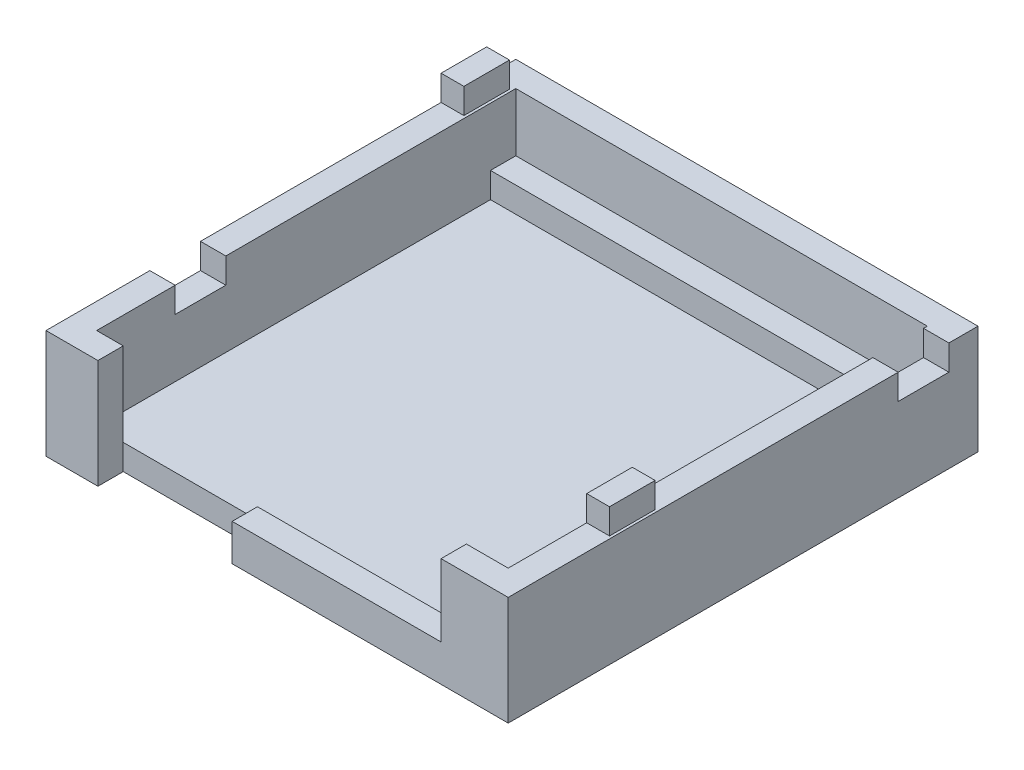
SolidWorks part; units mm, degrees
ref_plane "Front Plane" through (0, 0, 0) normal (0, 0, 1) x (1, 0, 0)
ref_plane "Top Plane" through (0, 0, 0) normal (0, 1, 0) x (1, 0, 0)
ref_plane "Right Plane" through (0, 0, 0) normal (1, 0, 0) x (0, 0, -1)
sketch "Sketch3" plane through (0, 0, 0) normal (0, 1, 0) x (1, 0, 0)
  line L1 (0, 0) -> (36.5, 0)
  line L2 (0, 0) -> (0, -37.1)
  line L3 (0, -37.1) -> (36.5, -37.1)
  line L4 (36.5, 0) -> (36.5, -37.1)
  dimension "D1" = 37.1
  dimension "D2" = 36.5
extrude "Shell" add sketch "Sketch3" along normal blind 8.6
sketch "Sketch4" plane through (0, 8.6, 0) normal (0, 1, 0) x (1, 0, 0)
  line L0 (36.5, 0) -> (0, 0) construction
  line L1 (2, -4) -> (34.5, -4)
  line L2 (2, -4) -> (2, -35.1)
  line L3 (2, -35.1) -> (34.5, -35.1)
  line L4 (34.5, -4) -> (34.5, -35.1)
  line L5 (36.5, -37.1) -> (36.5, 0) construction
  line L6 (0, 0) -> (0, -37.1) construction
  line L7 (0, -37.1) -> (36.5, -37.1) construction
  dimension "D1" = 4
  dimension "D2" = 2
  dimension "D3" = 2
  dimension "D4" = 2
extrude "Main Cavity" cut sketch "Sketch4" against normal offset from surface (6.6 mm away) 2 up to face at (18.25, 0, 18.55)
sketch "Sketch5" plane through (0, 8.6, 0) normal (0, 1, 0) x (1, 0, 0)
  line L0 (34.5, -35.1) -> (34.5, -4) construction
  line L1 (2, -4) -> (34.5, -4)
  line L2 (2, -4) -> (2, -2)
  line L3 (2, -2) -> (34.5, -2)
  line L4 (34.5, -4) -> (34.5, -2)
  dimension "D1" = 2
extrude "Support Shelf" cut sketch "Sketch5" against normal offset from surface (4.6 mm away) 2 up to face at (18.25, 2, 19.55)
sketch "Sketch6" plane through (0, 0, 37.1) normal (0, 0, 1) x (1, 0, 0)
  line L0 (0, 0) -> (36.5, 0) construction
  line L2 (31.2, 2.9) -> (31.2, 8.6)
  line L10 (14.7, 0) -> (4.1, 0)
  line L13 (4.1, 0) -> (4.1, 8.6)
  line L14 (0, 8.6) -> (0, 0) construction
  line L18 (14.7, 0) -> (14.7, 2.9)
  line L19 (14.7, 2.9) -> (31.2, 2.9)
  line L20 (31.2, 8.6) -> (4.1, 8.6)
  dimension "D1" = 4.1
  dimension "D2" = 2.9
  dimension "D6" = 10.6
extrude "Terminal Input" cut sketch "Sketch6" against normal up to surface (2 mm away) up to face at (18.25, 5.3, 35.1)
sketch "Sketch7" plane through (0, 8.6, 0) normal (0, 1, 0) x (1, 0, 0)
  line L0 (2, -2) -> (2, -35.1) construction
  line L1 (34.5, -25.3) -> (36.3, -25.3)
  line L2 (34.5, -25.3) -> (34.5, -28.9)
  line L3 (34.5, -28.9) -> (36.3, -28.9)
  line L4 (36.3, -25.3) -> (36.3, -28.9)
  line L5 (0, -2.3) -> (1.8, -2.3)
  line L6 (0, -2.3) -> (0, -5.9)
  line L7 (0, -5.9) -> (1.8, -5.9)
  line L8 (1.8, -2.3) -> (1.8, -5.9)
  line L9 (36.5, -37.1) -> (36.5, 0) construction
  line L15 (36.5, 0) -> (0, 0) construction
  line L16 (31.2, -37.1) -> (36.5, -37.1) construction
  point P12 (36.3, -27.1)
  point P13 (0, 0)
  point P14 (0, 0)
  dimension "D1" = 2.3
  dimension "D2" = 3.6
  dimension "D3" = 1.8
  dimension "D4" = 8.2
  dimension "D5" = 1.8
  dimension "D6" = 0.2
  dimension "D7" = 0.2
extrude "Male Tabs" add sketch "Sketch7" along normal blind 2
sketch "Sketch8" plane through (0, 8.6, 0) normal (0, 1, 0) x (1, 0, 0)
  line L0 (1.8, -2.3) -> (0, -2.3) construction
  line L1 (34.5, -2.3) -> (36.5, -2.3)
  line L2 (34.5, -2.3) -> (34.5, -6.3)
  line L3 (34.5, -6.3) -> (36.5, -6.3)
  line L4 (36.5, -2.3) -> (36.5, -6.3)
  line L5 (0, -24.9) -> (2, -24.9)
  line L6 (0, -24.9) -> (0, -28.9)
  line L7 (0, -28.9) -> (2, -28.9)
  line L8 (2, -24.9) -> (2, -28.9)
  line L9 (36.5, -37.1) -> (36.5, 0) construction
  line L11 (34.5, -4) -> (34.5, -35.1) construction
  line L12 (0, -5.9) -> (0, -37.1) construction
  line L13 (2, -2) -> (2, -35.1) construction
  line L14 (34.5, -28.9) -> (36.3, -28.9) construction
  dimension "D1" = 4
  dimension "D2" = 4
extrude "Female Tabs" cut sketch "Sketch8" against normal blind 2
